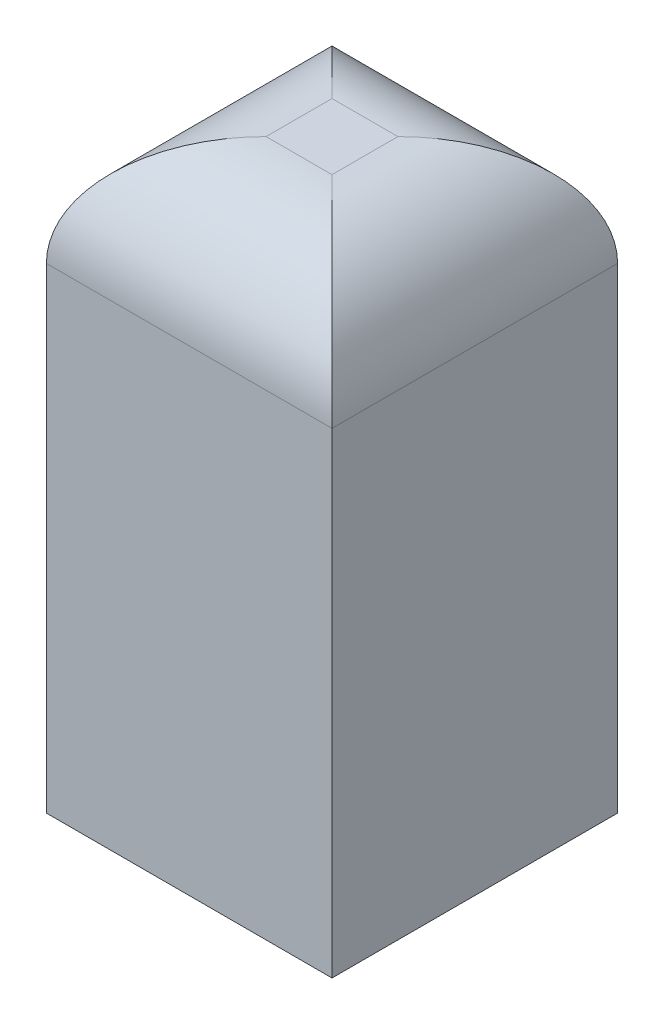
SolidWorks part; units mm, degrees
ref_plane "Front Plane" through (0, 0, 0) normal (0, 0, 1) x (1, 0, 0)
ref_plane "Top Plane" through (0, 0, 0) normal (0, 1, 0) x (1, 0, 0)
ref_plane "Right Plane" through (0, 0, 0) normal (1, 0, 0) x (0, 0, -1)
sketch "Sketch1" plane through (0, 0, 0) normal (0, 1, 0) x (1, 0, 0)
  line L1 (-1.95, 1.95) -> (1.95, 1.95)
  line L2 (-1.95, 1.95) -> (-1.95, -1.95)
  line L3 (-1.95, -1.95) -> (1.95, -1.95)
  line L4 (1.95, 1.95) -> (1.95, -1.95)
  line L5 (-1.95, 1.95) -> (1.95, -1.95) construction
  line L6 (-1.95, -1.95) -> (1.95, 1.95) construction
  point P0 (0, 0)
  dimension "D1" = 3.9
extrude "Boss-Extrude1" add sketch "Sketch1" along normal blind 8
fillet "Fillet1" radius 1.5 4 edges at (0, 8, 1.95) (-1.95, 8, 0) (0, 8, -1.95) (1.95, 8, 0)
